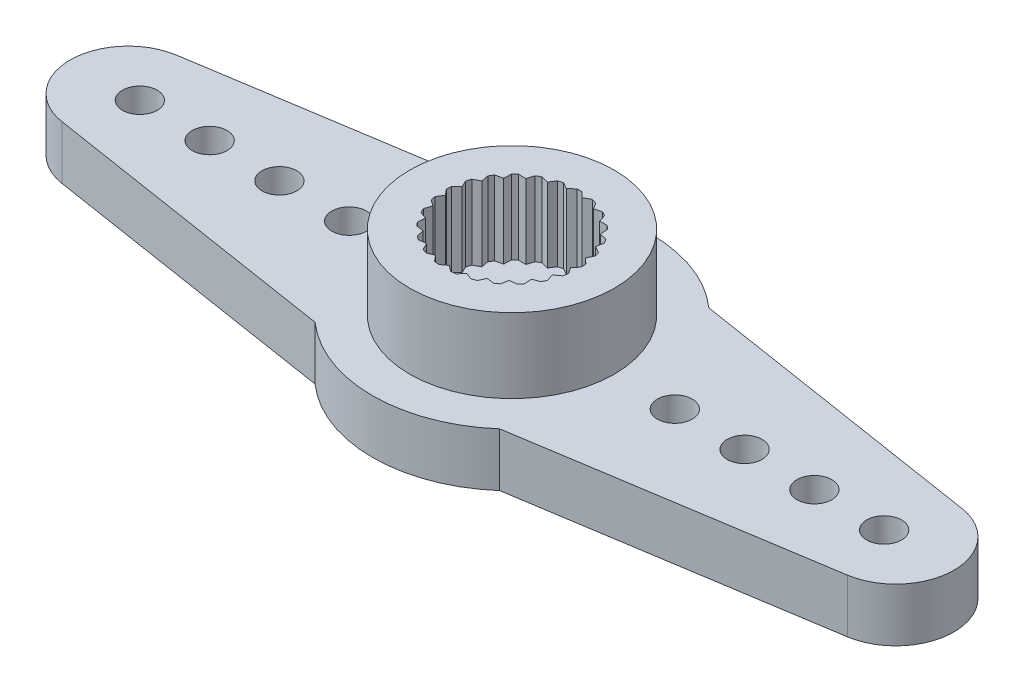
SolidWorks part; units mm, degrees
material "ABS"
ref_plane "Front Plane" through (0, 0, 0) normal (0, 0, 1) x (1, 0, 0)
ref_plane "Top Plane" through (0, 0, 0) normal (0, 1, 0) x (1, 0, 0)
ref_plane "Right Plane" through (0, 0, 0) normal (1, 0, 0) x (0, 0, -1)
sketch "Sketch2" plane through (0, 0, 0) normal (0, 1, 0) x (1, 0, 0)
  circle A0 centre (0, 0) radius 6
  circle A1 centre (0, 0) radius 1.5
  dimension "D1" = 12
  dimension "D2" = 3
extrude "Boss-Extrude1" add sketch "Sketch2" along normal mid plane 2.3
sketch "Sketch3" plane through (0, 1.15, 0) normal (0, 1, 0) x (1, 0, 0)
  line L0 (0, 0) -> (0, 2.9) construction
  line L3 (0, 0) -> (0.376, 2.9763) construction
  line L52 (0.1074, 2.898) -> (0.3384, 2.6787)
  line L53 (-0.1074, 2.898) -> (-0.3384, 2.6787)
  line L54 (0.8248, 2.7802) -> (0.9939, 2.5104)
  line L55 (0.6167, 2.8337) -> (0.3384, 2.6787)
  line L56 (1.4903, 2.4878) -> (1.587, 2.1843)
  line L57 (1.302, 2.5913) -> (0.9939, 2.5104)
  line L58 (2.0621, 2.039) -> (2.0804, 1.721)
  line L59 (1.9055, 2.1861) -> (1.587, 2.1843)
  line L60 (2.5044, 1.4621) -> (2.443, 1.1496)
  line L61 (2.3893, 1.6435) -> (2.0804, 1.721)
  line L62 (2.7894, 0.7934) -> (2.6522, 0.5059)
  line L63 (2.723, 0.9977) -> (2.443, 1.1496)
  line L64 (2.899, 0.0748) -> (2.6947, -0.1695)
  line L65 (2.8855, 0.2892) -> (2.6522, 0.5059)
  line L66 (2.8265, -0.6486) -> (2.5679, -0.8343)
  line L67 (2.8668, -0.4375) -> (2.6947, -0.1695)
  line L68 (2.5765, -1.3311) -> (2.2797, -1.4467)
  line L69 (2.6679, -1.1367) -> (2.5679, -0.8343)
  line L70 (2.1645, -1.93) -> (1.8483, -1.9682)
  line L71 (2.3014, -1.7645) -> (2.2797, -1.4467)
  line L72 (1.6165, -2.4077) -> (1.3007, -2.366)
  line L73 (1.7903, -2.2814) -> (1.8483, -1.9682)
  line L74 (0.967, -2.734) -> (0.6715, -2.6152)
  line L75 (1.1667, -2.655) -> (1.3007, -2.366)
  line L76 (0.2566, -2.8886) -> (0, -2.7)
  line L77 (0.4698, -2.8617) -> (0.6715, -2.6152)
  line L78 (-0.4698, -2.8617) -> (-0.6715, -2.6152)
  line L79 (-0.2566, -2.8886) -> (0, -2.7)
  line L80 (-1.1667, -2.655) -> (-1.3007, -2.366)
  line L81 (-0.967, -2.734) -> (-0.6715, -2.6152)
  line L82 (-1.7903, -2.2814) -> (-1.8483, -1.9682)
  line L83 (-1.6165, -2.4077) -> (-1.3007, -2.366)
  line L84 (-2.3014, -1.7645) -> (-2.2797, -1.4467)
  line L85 (-2.1645, -1.93) -> (-1.8483, -1.9682)
  line L86 (-2.6679, -1.1367) -> (-2.5679, -0.8343)
  line L87 (-2.5765, -1.3311) -> (-2.2797, -1.4467)
  line L88 (-2.8668, -0.4375) -> (-2.6947, -0.1695)
  line L89 (-2.8265, -0.6486) -> (-2.5679, -0.8343)
  line L90 (-2.8855, 0.2892) -> (-2.6522, 0.5059)
  line L91 (-2.899, 0.0748) -> (-2.6947, -0.1695)
  line L92 (-2.723, 0.9977) -> (-2.443, 1.1496)
  line L93 (-2.7894, 0.7934) -> (-2.6522, 0.5059)
  line L94 (-2.3893, 1.6435) -> (-2.0804, 1.721)
  line L95 (-2.5044, 1.4621) -> (-2.443, 1.1496)
  line L96 (-1.9055, 2.1861) -> (-1.587, 2.1843)
  line L97 (-2.0621, 2.039) -> (-2.0804, 1.721)
  line L98 (-1.302, 2.5913) -> (-0.9939, 2.5104)
  line L99 (-1.4903, 2.4878) -> (-1.587, 2.1843)
  line L100 (-0.6167, 2.8337) -> (-0.3384, 2.6787)
  line L101 (-0.8248, 2.7802) -> (-0.9939, 2.5104)
  line L102 (-2.533, 1.6075) -> (-2.3893, 1.6435) construction
  line L103 (-2.533, 1.6075) -> (-2.5044, 1.4621) construction
  line L104 (-2.8532, 0.9271) -> (-2.723, 0.9977) construction
  line L105 (-2.8532, 0.9271) -> (-2.7894, 0.7934) construction
  line L106 (-2.9941, 0.1884) -> (-2.8855, 0.2892) construction
  line L107 (-2.9941, 0.1884) -> (-2.899, 0.0748) construction
  line L108 (-2.9469, -0.5621) -> (-2.8668, -0.4375) construction
  line L109 (-2.9469, -0.5621) -> (-2.8265, -0.6486) construction
  line L110 (0, 3) -> (0.1074, 2.898) construction
  line L111 (0, 2.9) -> (0, 3) construction
  line L112 (0, 3) -> (-0.1074, 2.898) construction
  line L113 (-0.7461, 2.9057) -> (-0.6167, 2.8337) construction
  line L114 (-0.7461, 2.9057) -> (-0.8248, 2.7802) construction
  line L115 (-1.4453, 2.6289) -> (-1.302, 2.5913) construction
  line L116 (-1.4453, 2.6289) -> (-1.4903, 2.4878) construction
  line L117 (-2.0536, 2.1869) -> (-1.9055, 2.1861) construction
  line L118 (-2.0536, 2.1869) -> (-2.0621, 2.039) construction
  line L119 (-2.7145, -1.2773) -> (-2.6679, -1.1367) construction
  line L120 (-2.7145, -1.2773) -> (-2.5765, -1.3311) construction
  line L121 (-2.3115, -1.9123) -> (-2.3014, -1.7645) construction
  line L122 (-2.3115, -1.9123) -> (-2.1645, -1.93) construction
  line L123 (-1.7634, -2.4271) -> (-1.7903, -2.2814) construction
  line L124 (-1.7634, -2.4271) -> (-1.6165, -2.4077) construction
  line L125 (-1.1044, -2.7893) -> (-1.1667, -2.655) construction
  line L126 (-1.1044, -2.7893) -> (-0.967, -2.734) construction
  line L127 (-0.376, -2.9763) -> (-0.4698, -2.8617) construction
  line L128 (-0.376, -2.9763) -> (-0.2566, -2.8886) construction
  line L129 (0.376, -2.9763) -> (0.2566, -2.8886) construction
  line L130 (0.376, -2.9763) -> (0.4698, -2.8617) construction
  line L131 (1.1044, -2.7893) -> (0.967, -2.734) construction
  line L132 (1.1044, -2.7893) -> (1.1667, -2.655) construction
  line L133 (1.7634, -2.4271) -> (1.6165, -2.4077) construction
  line L134 (1.7634, -2.4271) -> (1.7903, -2.2814) construction
  line L135 (2.3115, -1.9123) -> (2.3014, -1.7645) construction
  line L136 (2.3115, -1.9123) -> (2.1645, -1.93) construction
  line L137 (2.7145, -1.2773) -> (2.6679, -1.1367) construction
  line L138 (2.7145, -1.2773) -> (2.5765, -1.3311) construction
  line L139 (2.9469, -0.5621) -> (2.8668, -0.4375) construction
  line L140 (2.9469, -0.5621) -> (2.8265, -0.6486) construction
  line L141 (2.9941, 0.1884) -> (2.8855, 0.2892) construction
  line L142 (2.9941, 0.1884) -> (2.899, 0.0748) construction
  line L143 (2.8532, 0.9271) -> (2.723, 0.9977) construction
  line L144 (2.8532, 0.9271) -> (2.7894, 0.7934) construction
  line L145 (2.533, 1.6075) -> (2.3893, 1.6435) construction
  line L146 (2.533, 1.6075) -> (2.5044, 1.4621) construction
  line L147 (2.0536, 2.1869) -> (1.9055, 2.1861) construction
  line L148 (2.0536, 2.1869) -> (2.0621, 2.039) construction
  line L149 (1.4453, 2.6289) -> (1.302, 2.5913) construction
  line L150 (1.4453, 2.6289) -> (1.4903, 2.4878) construction
  line L151 (0.7461, 2.9057) -> (0.6167, 2.8337) construction
  line L152 (0.7461, 2.9057) -> (0.8248, 2.7802) construction
  circle A0 centre (0, 0) radius 4.4
  circle A1 centre (0, 0) radius 3 construction
  circle A2 centre (0, 0) radius 2.7 construction
  arc A3 (-0.6167, 2.8337) -> (-0.8248, 2.7802) centre (0, 0) ccw
  arc A4 (-0.1074, 2.898) -> (-0.6167, 2.8337) centre (0, 0) ccw construction
  arc A5 (-0.8248, 2.7802) -> (-1.302, 2.5913) centre (0, 0) ccw construction
  arc A6 (-1.302, 2.5913) -> (-1.4903, 2.4878) centre (0, 0) ccw
  arc A7 (-1.4903, 2.4878) -> (-1.9055, 2.1861) centre (0, 0) ccw construction
  arc A8 (-1.9055, 2.1861) -> (-2.0621, 2.039) centre (0, 0) ccw
  arc A9 (-2.0621, 2.039) -> (-2.3893, 1.6435) centre (0, 0) ccw construction
  arc A10 (-2.3893, 1.6435) -> (-2.5044, 1.4621) centre (0, 0) ccw
  arc A11 (-2.5044, 1.4621) -> (-2.723, 0.9977) centre (0, 0) ccw construction
  arc A12 (-2.723, 0.9977) -> (-2.7894, 0.7934) centre (0, 0) ccw
  arc A13 (-2.7894, 0.7934) -> (-2.8855, 0.2892) centre (0, 0) ccw construction
  arc A14 (-2.8855, 0.2892) -> (-2.899, 0.0748) centre (0, 0) ccw
  arc A15 (-2.899, 0.0748) -> (-2.8668, -0.4375) centre (0, 0) ccw construction
  arc A16 (-2.8668, -0.4375) -> (-2.8265, -0.6486) centre (0, 0) ccw
  arc A17 (-2.8265, -0.6486) -> (-2.6679, -1.1367) centre (0, 0) ccw construction
  arc A18 (-2.6679, -1.1367) -> (-2.5765, -1.3311) centre (0, 0) ccw
  arc A19 (-2.5765, -1.3311) -> (-2.3014, -1.7645) centre (0, 0) ccw construction
  arc A20 (-2.3014, -1.7645) -> (-2.1645, -1.93) centre (0, 0) ccw
  arc A21 (-2.1645, -1.93) -> (-1.7903, -2.2814) centre (0, 0) ccw construction
  arc A22 (-1.7903, -2.2814) -> (-1.6165, -2.4077) centre (0, 0) ccw
  arc A23 (-1.6165, -2.4077) -> (-1.1667, -2.655) centre (0, 0) ccw construction
  arc A24 (-1.1667, -2.655) -> (-0.967, -2.734) centre (0, 0) ccw
  arc A25 (-0.967, -2.734) -> (-0.4698, -2.8617) centre (0, 0) ccw construction
  arc A26 (-0.4698, -2.8617) -> (-0.2566, -2.8886) centre (0, 0) ccw
  arc A27 (-0.2566, -2.8886) -> (0.2566, -2.8886) centre (0, 0) ccw construction
  arc A28 (0.2566, -2.8886) -> (0.4698, -2.8617) centre (0, 0) ccw
  arc A29 (0.4698, -2.8617) -> (0.967, -2.734) centre (0, 0) ccw construction
  arc A30 (0.967, -2.734) -> (1.1667, -2.655) centre (0, 0) ccw
  arc A31 (1.1667, -2.655) -> (1.6165, -2.4077) centre (0, 0) ccw construction
  arc A32 (1.6165, -2.4077) -> (1.7903, -2.2814) centre (0, 0) ccw
  arc A33 (1.7903, -2.2814) -> (2.1645, -1.93) centre (0, 0) ccw construction
  arc A34 (2.1645, -1.93) -> (2.3014, -1.7645) centre (0, 0) ccw
  arc A35 (2.3014, -1.7645) -> (2.5765, -1.3311) centre (0, 0) ccw construction
  arc A36 (2.5765, -1.3311) -> (2.6679, -1.1367) centre (0, 0) ccw
  arc A37 (2.6679, -1.1367) -> (2.8265, -0.6486) centre (0, 0) ccw construction
  arc A38 (2.8265, -0.6486) -> (2.8668, -0.4375) centre (0, 0) ccw
  arc A39 (2.8668, -0.4375) -> (2.899, 0.0748) centre (0, 0) ccw construction
  arc A40 (2.899, 0.0748) -> (2.8855, 0.2892) centre (0, 0) ccw
  arc A41 (2.8855, 0.2892) -> (2.7894, 0.7934) centre (0, 0) ccw construction
  arc A42 (2.7894, 0.7934) -> (2.723, 0.9977) centre (0, 0) ccw
  arc A43 (2.723, 0.9977) -> (2.5044, 1.4621) centre (0, 0) ccw construction
  arc A44 (2.5044, 1.4621) -> (2.3893, 1.6435) centre (0, 0) ccw
  arc A45 (2.3893, 1.6435) -> (2.0621, 2.039) centre (0, 0) ccw construction
  arc A46 (2.0621, 2.039) -> (1.9055, 2.1861) centre (0, 0) ccw
  arc A47 (1.9055, 2.1861) -> (1.4903, 2.4878) centre (0, 0) ccw construction
  arc A48 (1.4903, 2.4878) -> (1.302, 2.5913) centre (0, 0) ccw
  arc A49 (1.302, 2.5913) -> (0.8248, 2.7802) centre (0, 0) ccw construction
  arc A50 (0.8248, 2.7802) -> (0.6167, 2.8337) centre (0, 0) ccw
  arc A51 (0.3635, 2.8771) -> (0.1074, 2.898) centre (0, 0) ccw construction
  arc A52 (0.1074, 2.898) -> (-0.1074, 2.898) centre (0, 0) ccw
  arc A53 (0.6167, 2.8337) -> (0.3635, 2.8771) centre (0, 0) ccw construction
  point P84 (0, 0)
  dimension "D1" = 8.8
  dimension "D2" = 5.4
  dimension "D3" = 6
  dimension "D6" = 5.8
  dimension "D4" = 7.2
  dimension "D5" = 25
extrude "Boss-Extrude2" add sketch "Sketch3" along normal blind 3.2
sketch "Sketch4" plane through (0, 0, 0) normal (0, 1, 0) x (1, 0, 0)
  line L0 (0, 0) -> (16, 0) construction
  line L1 (3.9686, 4.5) -> (16.8881, 2.4697)
  line L2 (3.9686, -4.5) -> (16.8881, -2.4697)
  line L3 (16, 0) -> (13, 0) construction
  circle A0 centre (0, 0) radius 6 construction
  arc A1 (3.9686, -4.5) -> (3.9686, 4.5) centre (0, 0) ccw
  arc A2 (16.8881, 2.4697) -> (16.8881, -2.4697) centre (16.5, 0) cw
  circle A3 centre (16, 0) radius 0.75
  circle A4 centre (13, 0) radius 0.75
  circle A5 centre (10, 0) radius 0.75
  circle A6 centre (7, 0) radius 0.75
  dimension "D3" = 2.5
  dimension "D5" = 1.5
  dimension "D2" = 9
  dimension "D7" = 3
  dimension "D4" = 0.5
  dimension "D1" = 16
  dimension "D6" = 4
extrude "Boss-Extrude3" add sketch "Sketch4" along normal mid plane 2.3
pattern_circular "CirPattern1" count 2 over 360 about axis through (0, 0, 0) along (0, 1, 0) of "Boss-Extrude3"
sketch "Sketch5" [suppressed] plane through (0, 0, 0) normal (0, 1, 0) x (1, 0, 0)
  line L0 (3, 7) -> (-3, 7) construction
  circle A0 centre (0, 0) radius 10
  circle A1 centre (0, 7) radius 0.75
  circle A2 centre (-3, 7) radius 0.75
  circle A3 centre (3, 7) radius 0.75
  circle A4 centre (7, 3) radius 0.75
  circle A5 centre (7, 0) radius 0.75
  circle A6 centre (7, -3) radius 0.75
  circle A7 centre (3, -7) radius 0.75
  circle A8 centre (0, -7) radius 0.75
  circle A9 centre (-3, -7) radius 0.75
  circle A10 centre (-7, -3) radius 0.75
  circle A11 centre (-7, 0) radius 0.75
  circle A12 centre (-7, 3) radius 0.75
  circle A13 centre (0, 0) radius 1.5 construction
  circle A14 centre (0, 0) radius 1.5
  point P8 (0, 7)
  point P31 (0, 0)
  dimension "D1" = 1.5
  dimension "D3" = 2.25
  dimension "D4" = 6
  dimension "D2" = 7
  dimension "D5" = 4
extrude "Boss-Extrude4" [suppressed] add sketch "Sketch5" along normal mid plane 2.3
equation "\"N_hole\"= 4"
equation "\"N_horn\"= 2"
equation "\"D6@Sketch4\"=\"N_hole\""
equation "\"D1@CirPattern1\"=\"N_horn\""
equation "\"D1@Sketch4\"=(\"N_hole\" - 1) *3 +7"
